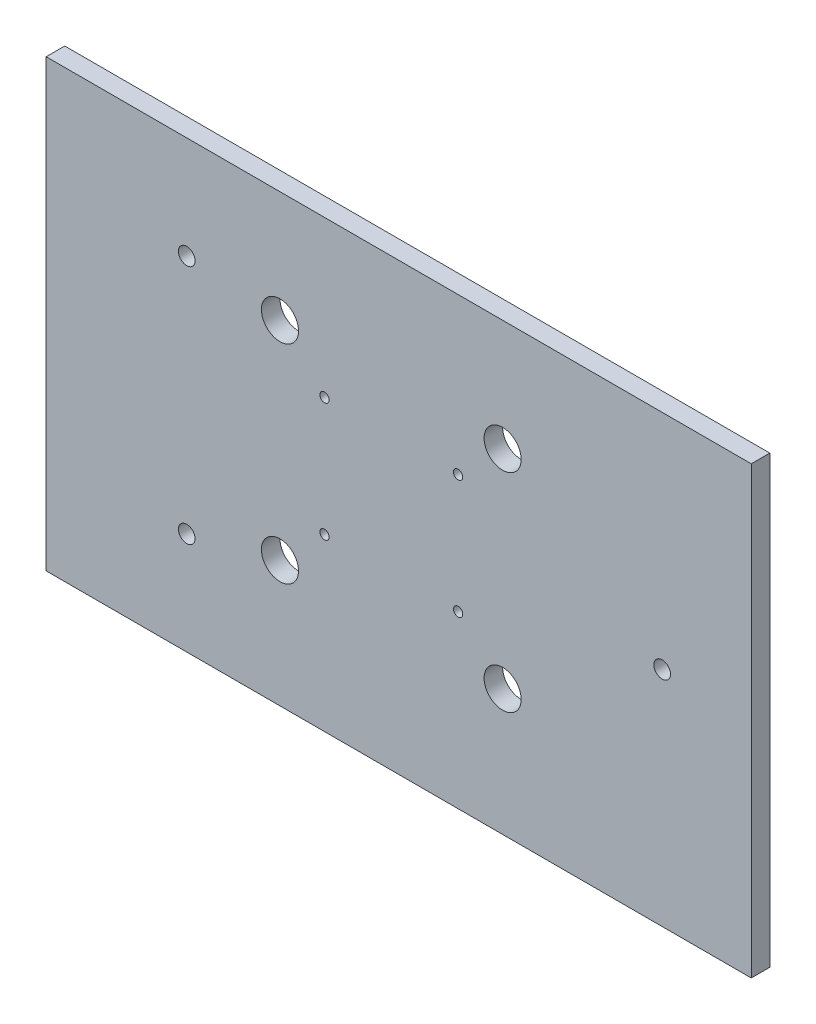
SolidWorks part; units mm, degrees
ref_plane "Alzado" through (0, 0, 0) normal (0, 0, 1) x (1, 0, 0)
ref_plane "Planta" through (0, 0, 0) normal (0, 1, 0) x (1, 0, 0)
ref_plane "Vista lateral" through (0, 0, 0) normal (1, 0, 0) x (0, 0, -1)
sketch "Croquis1" plane through (0, 0, 0) normal (0, 0, 1) x (1, 0, 0)
  line L0 (60.5, -27.5) -> (60.5, 92.5)
  line L1 (60.5, 92.5) -> (-129.5, 92.5)
  line L2 (-129.5, 92.5) -> (-129.5, -27.5)
  line L3 (60.5, -27.5) -> (-129.5, -27.5)
  circle A0 centre (36.5, 32.5) radius 2.25
  circle A1 centre (-91.6232, 0.0693) radius 2.25
  circle A2 centre (-91.6232, 64.9307) radius 2.25
  circle A7 centre (-66.5, 62.5) radius 5
  circle A8 centre (-6.5, 62.5) radius 5
  circle A9 centre (-6.5, 6.5) radius 5
  circle A10 centre (-66.5, 6.5) radius 5
  circle A11 centre (-54.5, 50.5) radius 1.25
  circle A12 centre (-18.5, 50.5) radius 1.25
  circle A13 centre (-18.5, 18.5) radius 1.25
  circle A14 centre (-54.5, 18.5) radius 1.25
  dimension "D8" = 4.5
  dimension "D9" = 10
  dimension "D10" = 10
  dimension "D13" = 56
  dimension "D14" = 60
  dimension "D15" = 4.5
  dimension "D16" = 4.5
  dimension "D11" = 10
  dimension "D12" = 10
  dimension "D18" = 30
  dimension "D19" = 67
  dimension "D1" = 24
  dimension "D2" = 60
  dimension "D3" = 27.5693
  dimension "D4" = 37.8768
  dimension "D5" = 37.8768
  dimension "D6" = 120
  dimension "D7" = 190
  dimension "D17" = 27.5693
  dimension "D20" = 120
  dimension "D21" = 190
extrude "Saliente-Extruir1" add sketch "Croquis1" along normal blind 5
